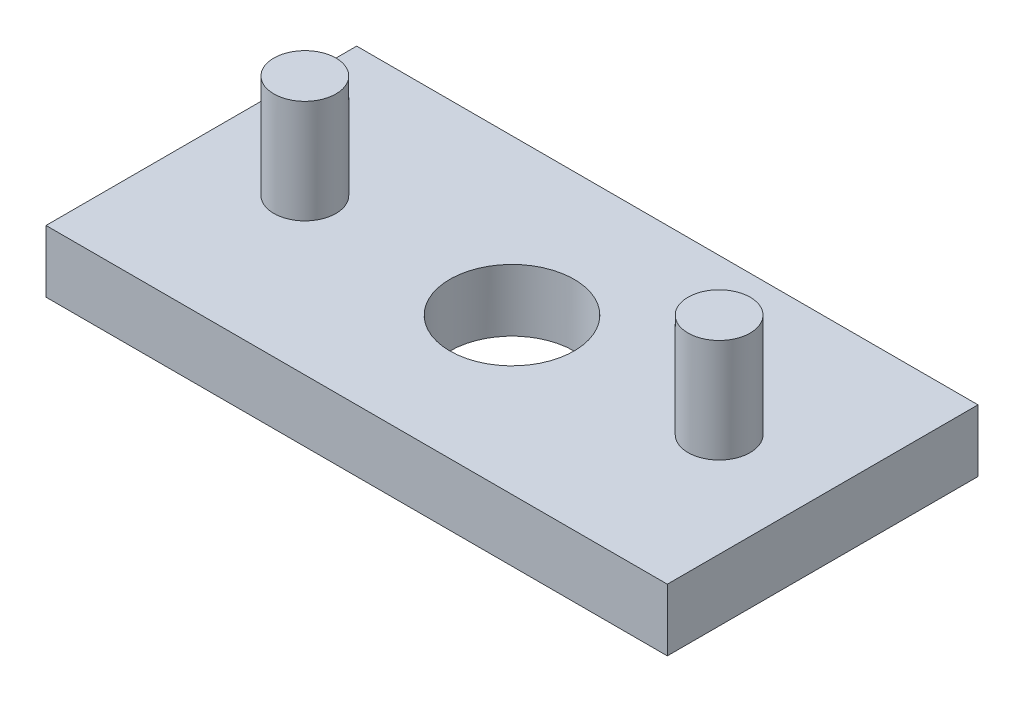
SolidWorks part; units mm, degrees
ref_plane "Front" through (0, 0, 0) normal (0, 0, 1) x (1, 0, 0)
ref_plane "Top" through (0, 0, 0) normal (0, 1, 0) x (1, 0, 0)
ref_plane "Right" through (0, 0, 0) normal (1, 0, 0) x (0, 0, -1)
sketch "草图1" plane through (0, 0, 0) normal (0, 1, 0) x (1, 0, 0)
  line L0 (-100, 0) -> (100, 0) construction
  line L1 (-150, -75) -> (150, -75)
  line L2 (-150, -75) -> (-150, 75)
  line L3 (-150, 75) -> (150, 75)
  line L4 (150, -75) -> (150, 75)
  line L5 (-150, -75) -> (150, 75) construction
  line L6 (-150, 75) -> (150, -75) construction
  line L7 (0, 42.3706) -> (0, -38.0109) construction
  point P0 (0, 0)
  dimension "D1" = 300
  dimension "D2" = 150
  dimension "D3" = 200
extrude "凸台-拉伸1" add sketch "草图1" along normal blind 30
sketch "草图2" plane through (0, 30, 0) normal (0, 1, 0) x (1, 0, 0)
  circle A0 centre (-100, 0) radius 15
  circle A1 centre (100, 0) radius 15
  dimension "D1" = 30
extrude "凸台-拉伸2" add sketch "草图2" along normal blind 50
sketch "草图3" plane through (0, 30, 0) normal (0, 1, 0) x (1, 0, 0)
  circle A0 centre (0, 0) radius 30
  dimension "D1" = 60
extrude "切除-拉伸1" cut sketch "草图3" against normal blind 50
